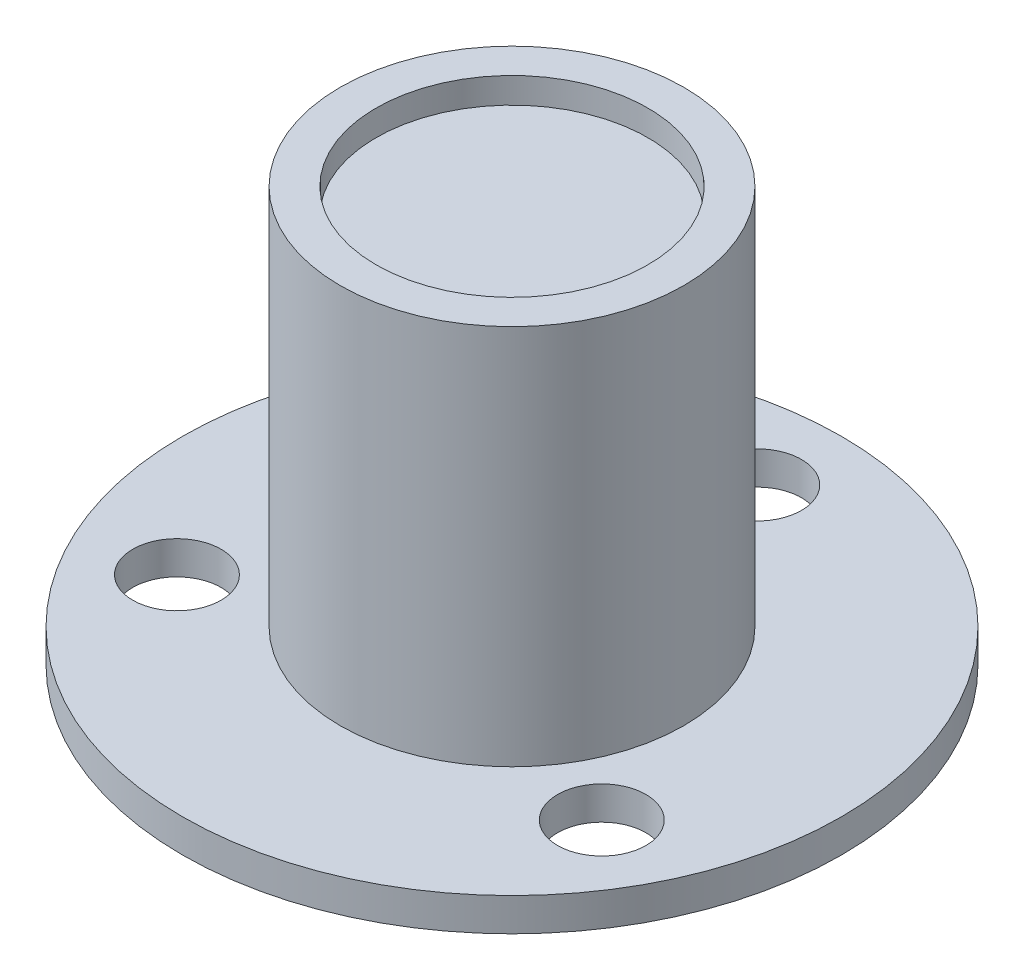
SolidWorks part; units mm, degrees
ref_plane "Front Plane" through (0, 0, 0) normal (0, 0, 1) x (1, 0, 0)
ref_plane "Top Plane" through (0, 0, 0) normal (0, 1, 0) x (1, 0, 0)
ref_plane "Right Plane" through (0, 0, 0) normal (1, 0, 0) x (0, 0, -1)
sketch "Sketch1" plane through (0, 0, 0) normal (0, 1, 0) x (1, 0, 0)
  circle A0 centre (0, 0) radius 6.22
  dimension "D1" = 12.44
extrude "Boss-Extrude1" add sketch "Sketch1" along normal blind 15 contours A0
sketch "Sketch2" plane through (0, 0, 0) normal (0, -1, 0) x (1, 0, 0)
  circle A0 centre (0, 0) radius 11.93
  point P3 (0, 0)
  dimension "D1" = 23.86
extrude "Boss-Extrude2" add sketch "Sketch2" against normal blind 1.2
sketch "Sketch3" plane through (0, 1.2, 0) normal (0, 1, 0) x (1, 0, 0)
  line L0 (0, 10.48) -> (0, 11.93) construction
  line L1 (9.0759, -5.24) -> (10.3317, -5.965) construction
  line L2 (-9.0759, -5.24) -> (-10.3317, -5.965) construction
  circle A0 centre (0, 8.88) radius 1.6
  circle A3 centre (0, 0) radius 11.93 construction
  circle A4 centre (7.6903, -4.44) radius 1.6
  circle A5 centre (-7.6903, -4.44) radius 1.6
  point P14 (0, 0)
  point P15 (-9.9467, -6.5869)
  dimension "D1" = 3.2
  dimension "D3" = 1.45
  dimension "D2" = 3
extrude "Cut-Extrude1" cut sketch "Sketch3" against normal up to next
sketch "Sketch4" plane through (0, 15, 0) normal (0, 1, 0) x (1, 0, 0)
  circle A0 centre (0, 0) radius 4.92
  dimension "D1" = 9.84
extrude "Cut-Extrude2" cut sketch "Sketch4" against normal blind 0.93
sketch "Sketch5" plane through (0, 0, 0) normal (0, -1, 0) x (1, 0, 0)
  circle A0 centre (0, 0) radius 4.875
  dimension "D1" = 9.75
extrude "Boss-Extrude3" add sketch "Sketch5" along normal blind 0.76
sketch "Sketch6" plane through (0, -0.76, 0) normal (0, -1, 0) x (1, 0, 0)
  circle A0 centre (0, 0) radius 2.425
  dimension "D1" = 4.85
extrude "Boss-Extrude4" add sketch "Sketch6" along normal offset from surface (1.88 mm away) 17.64 up to face at (0, 15, 4.92)
sketch "Sketch7" plane through (0, 0, 0) normal (0, -1, 0) x (1, 0, 0)
  circle A1 centre (0, 0) radius 4.875 construction
  circle A2 centre (0, 0) radius 5.445
  circle A3 centre (0, 0) radius 5.445
  circle A4 centre (0, 0) radius 4.875
  dimension "D1" = 0.57
extrude "Cut-Extrude3" cut sketch "Sketch7" against normal blind 0.25
